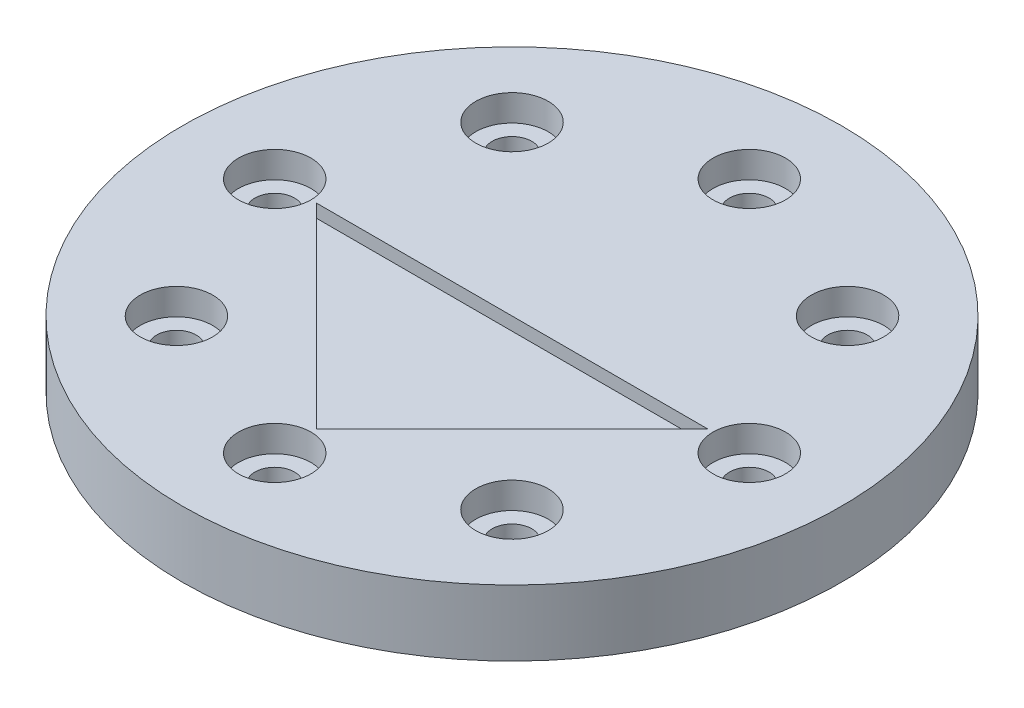
SolidWorks part; units mm, degrees
ref_plane "前视基准面" through (0, 0, 0) normal (0, 0, 1) x (1, 0, 0)
ref_plane "上视基准面" through (0, 0, 0) normal (0, 1, 0) x (1, 0, 0)
ref_plane "右视基准面" through (0, 0, 0) normal (1, 0, 0) x (0, 0, -1)
sketch "草图1" plane through (0, 0, 0) normal (0, 1, 0) x (1, 0, 0)
  circle A0 centre (0, 0) radius 25
  dimension "D1" = 50
extrude "凸台-拉伸2" add sketch "草图1" along normal blind 1
sketch "草图2" plane through (0, 1, 0) normal (0, 1, 0) x (1, 0, 0)
  circle A0 centre (18, 0) radius 1.5
  dimension "D2" = 3
extrude "切除-拉伸1" cut sketch "草图2" against normal blind 1
pattern_circular "阵列(圆周)1" count 8 over 360 about axis through (0, 0, 0) along (0, 1, 0) of "切除-拉伸1"
sketch "草图3" plane through (0, 1, 0) normal (0, 1, 0) x (1, 0, 0)
  line L0 (-15.2028, 0) -> (15.2028, 0)
  line L2 (15.2028, 0) -> (0, -15.2028)
  line L3 (0, -15.2028) -> (-15.2028, 0)
  dimension "D1" = 21.5
  dimension "D3" = 21.5
extrude "切除-拉伸2" cut sketch "草图3" against normal blind 1
sketch "草图4" plane through (0, 1, 0) normal (0, 1, 0) x (1, 0, 0)
  line L0 (0, -14.8492) -> (14.8492, 0)
  line L2 (15.2028, 0) -> (-15.2028, 0) construction
  line L4 (0, -14.8492) -> (-14.8492, 0)
  line L6 (-14.8492, 0) -> (-15.2028, 0)
  line L7 (-15.2028, 0) -> (0, -15.2028)
  line L8 (0, -15.2028) -> (15.2028, 0)
  line L9 (15.2028, 0) -> (14.8492, 0)
extrude "凸台-拉伸3" add sketch "草图4" against normal blind 1
sketch "草图5" plane through (0, 0, 0) normal (0, -1, 0) x (1, 0, 0)
  circle A0 centre (0, 0) radius 25
extrude "凸台-拉伸5" add sketch "草图5" along normal blind 2
sketch "草图6" plane through (0, 0, 0) normal (0, 1, 0) x (1, 0, 0)
  circle A0 centre (18, 0) radius 1.5
  dimension "D1" = 3
extrude "切除-拉伸3" cut sketch "草图6" against normal blind 2
pattern_circular "阵列(圆周)2" count 8 over 360 about axis through (0, 1, 0) along (0, -1, 0) of "切除-拉伸3"
sketch "草图7" plane through (0, 1, 0) normal (0, 1, 0) x (1, 0, 0)
  line L0 (-14.8492, 0) -> (14.8492, 0)
  line L1 (14.8492, 0) -> (0, -14.8492)
  line L2 (0, -14.8492) -> (-14.8492, 0)
  circle A0 centre (0, 0) radius 25
sketch "草图8" plane through (0, 1, 0) normal (0, 1, 0) x (1, 0, 0)
  circle A0 centre (18, 0) radius 2.75
  dimension "D1" = 5.5
extrude "凸台-拉伸6" add sketch "草图7" along normal blind 2
extrude "切除-拉伸4" cut sketch "草图8" along normal blind 2
pattern_circular "阵列(圆周)3" count 8 over 360 about axis through (0, 0, 0) along (0, 1, 0) of "切除-拉伸4"
sketch "草图9" plane through (0, 0, 0) normal (0, 1, 0) x (1, 0, 0)
  line L0 (-14.8492, 0) -> (14.8492, 0)
  line L1 (14.8492, 0) -> (0, -14.8492)
  line L2 (0, -14.8492) -> (-14.8492, 0)
extrude "凸台-拉伸8" add sketch "草图9" along normal blind 2
